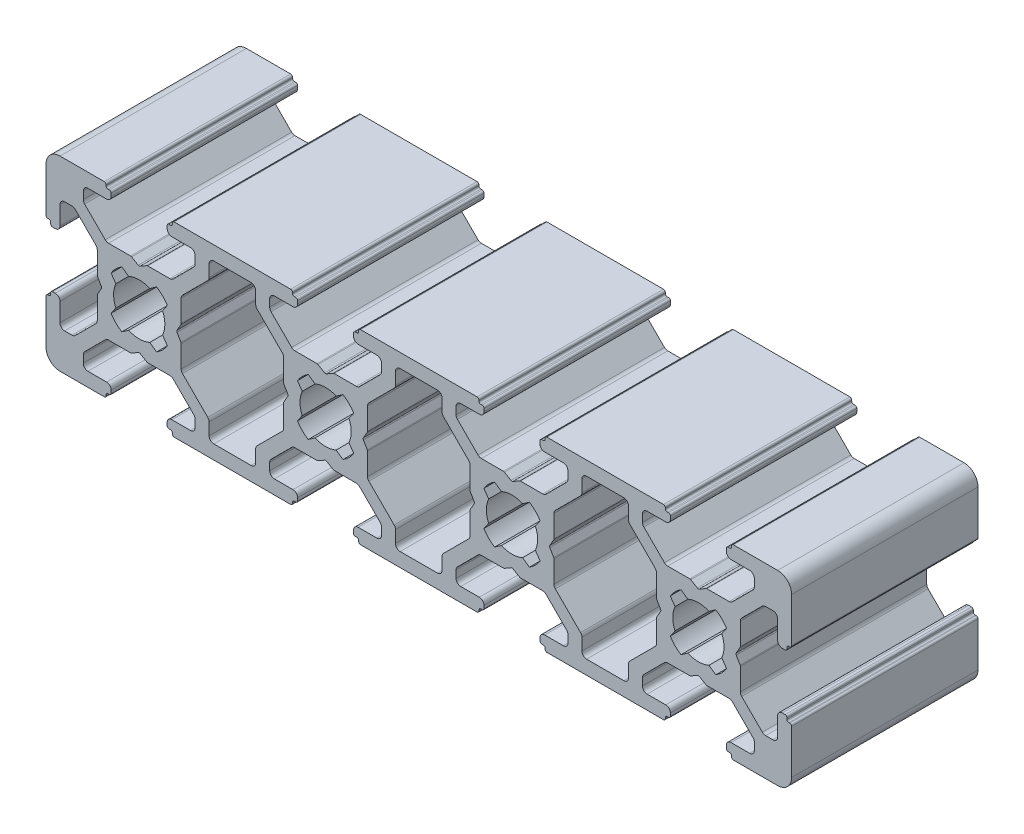
SolidWorks part; units mm, degrees
material "АД31Т ГОСТ 4784-97"
ref_plane "Спереди" through (0, 0, 0) normal (0, 0, 1) x (1, 0, 0)
ref_plane "Сверху" through (0, 0, 0) normal (0, 1, 0) x (1, 0, 0)
ref_plane "Справа" through (0, 0, 0) normal (1, 0, 0) x (0, 0, -1)
sketch "Эскиз1" plane through (0, 0, 0) normal (0, 0, 1) x (1, 0, 0)
  line L0 (3.1454, -5.8536) -> (2.6464, -6.3525)
  line L1 (5.5, 0.9196) -> (5.5, 3.2919)
  line L2 (-13.6454, 4.6464) -> (-15.8536, 6.8546)
  line L3 (-18, 6) -> (-17.2081, 6)
  line L4 (-14.5, 0.9196) -> (-14.5, 3.2919)
  line L5 (-6.3546, -4.6464) -> (-4.1464, -6.8546)
  line L6 (-19.3, 3) -> (-19, 3)
  line L7 (-19.5, 3.35) -> (-19.5, 3.2)
  line L8 (-19.8, 3.55) -> (-19.7, 3.55)
  line L9 (-20, 8.5) -> (-20, 3.75)
  line L10 (-13.0204, 1.8653) -> (-12.5065, 1.1313)
  line L11 (-18.5, 3.5) -> (-18.5, 5.5)
  line L12 (-13.75, 10) -> (-18.5, 10)
  line L13 (-14.6464, 3.6454) -> (-16.8546, 5.8536)
  line L14 (-10.9196, 4.5) -> (-13.2919, 4.5)
  line L15 (-16, 8) -> (-16, 7.2081)
  line L16 (-14.0577, -0.1) -> (-14.4732, -0.8196)
  line L17 (-14.0577, 0.1) -> (-14.4732, 0.8196)
  line L18 (-11.8653, 3.0204) -> (-11.1313, 2.5065)
  line L19 (6.25, 10) -> (-6.25, 10)
  line L20 (-8.1347, 3.0204) -> (-8.8687, 2.5065)
  line L21 (-5.5, -0.9196) -> (-5.5, -3.2919)
  line L22 (-6.7081, 4.5) -> (-9.0804, 4.5)
  line L23 (-2.5, 8) -> (-2.5, 6.7061)
  line L24 (-3.1454, 5.8536) -> (-2.6464, 6.3525)
  line L25 (-10.1, 4.0577) -> (-10.8196, 4.4732)
  line L26 (-6.9796, 1.8653) -> (-7.4935, 1.1313)
  line L27 (-6.9796, -1.8653) -> (-7.4935, -1.1313)
  line L28 (-8.1347, -3.0204) -> (-8.8687, -2.5065)
  line L29 (-11.8653, -3.0204) -> (-11.1313, -2.5065)
  line L30 (-13.0204, -1.8653) -> (-12.5065, -1.1313)
  line L31 (-9.9, 4.0577) -> (-9.1804, 4.4732)
  line L32 (-13.5, 8.5) -> (-15.5, 8.5)
  line L33 (-13.55, 9.8) -> (-13.55, 9.7)
  line L34 (-13.35, 9.5) -> (-13.2, 9.5)
  line L35 (-13, 9.3) -> (-13, 9)
  line L36 (-10.9196, 4.5) -> (-13.2919, 4.5)
  line L37 (2, 8.5) -> (-2, 8.5)
  line L38 (-7, 9.3) -> (-7, 9)
  line L39 (-5.3536, 3.6454) -> (-3.1454, 5.8536)
  line L40 (-4, 8) -> (-4, 7.2081)
  line L41 (-6.3546, 4.6464) -> (-4.1464, 6.8546)
  line L42 (-6.65, 9.5) -> (-6.8, 9.5)
  line L43 (-6.45, 9.8) -> (-6.45, 9.7)
  line L44 (-6.5, 8.5) -> (-4.5, 8.5)
  line L45 (5.9423, -0.1) -> (5.5268, -0.8196)
  line L46 (-6.3546, -4.6464) -> (-4.1464, -6.8546)
  line L47 (-5.3536, -3.6454) -> (-3.1454, -5.8536)
  line L48 (-6.5, -8.5) -> (-4.5, -8.5)
  line L49 (-6.45, -9.8) -> (-6.45, -9.7)
  line L50 (-6.65, -9.5) -> (-6.8, -9.5)
  line L51 (-4, -8) -> (-4, -7.2081)
  line L52 (-5.3536, -3.6454) -> (-3.1454, -5.8536)
  line L53 (-7, -9.3) -> (-7, -9)
  line L54 (2, -8.5) -> (-2, -8.5)
  line L55 (-10.9196, -4.5) -> (-13.2919, -4.5)
  line L56 (-13, -9.3) -> (-13, -9)
  line L57 (-13.35, -9.5) -> (-13.2, -9.5)
  line L58 (-13.55, -9.8) -> (-13.55, -9.7)
  line L59 (-13.5, -8.5) -> (-15.5, -8.5)
  line L60 (-9.9, -4.0577) -> (-9.1804, -4.4732)
  line L61 (-13.0204, 1.8653) -> (-12.5065, 1.1313)
  line L62 (-11.8653, 3.0204) -> (-11.1313, 2.5065)
  line L63 (-8.1347, 3.0204) -> (-8.8687, 2.5065)
  line L64 (-6.9796, 1.8653) -> (-7.4935, 1.1313)
  line L65 (-6.9796, -1.8653) -> (-7.4935, -1.1313)
  line L66 (-10.1, -4.0577) -> (-10.8196, -4.4732)
  line L67 (-2.5, -8) -> (-2.5, -6.7061)
  line L68 (-6.7081, -4.5) -> (-9.0804, -4.5)
  line L69 (-5.9423, 0.1) -> (-5.5268, 0.8196)
  line L70 (-8.1347, -3.0204) -> (-8.8687, -2.5065)
  line L71 (-11.8653, -3.0204) -> (-11.1313, -2.5065)
  line L72 (-14.0577, -0.1) -> (-14.4732, -0.8196)
  line L73 (-14.0577, 0.1) -> (-14.4732, 0.8196)
  line L74 (-16, -8) -> (-16, -7.2081)
  line L75 (-10.9196, -4.5) -> (-13.2919, -4.5)
  line L76 (-14.6464, -3.6454) -> (-16.8546, -5.8536)
  line L77 (-13.75, -10) -> (-18.5, -10)
  line L78 (-18.5, -3.5) -> (-18.5, -5.5)
  line L79 (-13.0204, -1.8653) -> (-12.5065, -1.1313)
  line L80 (-20, -8.5) -> (-20, -3.75)
  line L81 (-19.8, -3.55) -> (-19.7, -3.55)
  line L82 (-19.5, -3.35) -> (-19.5, -3.2)
  line L83 (-19.3, -3) -> (-19, -3)
  line L84 (-14.5, -0.9196) -> (-14.5, -3.2919)
  line L85 (-18, -6) -> (-17.2081, -6)
  line L86 (-13.6454, -4.6464) -> (-15.8536, -6.8546)
  line L87 (6.25, -10) -> (-6.25, -10)
  line L88 (-5.3536, -3.6454) -> (-3.1454, -5.8536)
  line L89 (-5.9423, -0.1) -> (-5.5268, -0.8196)
  line L90 (-5.9423, 0.1) -> (-5.5268, 0.8196)
  line L91 (-5.9423, -0.1) -> (-5.5268, -0.8196)
  line L92 (-5.5, 0.9196) -> (-5.5, 3.2919)
  line L93 (-3.1454, -5.8536) -> (-2.6464, -6.3525)
  line L94 (5.9423, 0.1) -> (5.5268, 0.8196)
  line L95 (5.9423, -0.1) -> (5.5268, -0.8196)
  line L96 (5.3536, -3.6454) -> (3.1454, -5.8536)
  line L97 (13.6454, -4.6464) -> (15.8536, -6.8546)
  line L99 (14.5, -0.9196) -> (14.5, -3.2919)
  line L100 (13.75, 10) -> (26.25, 10)
  line L101 (13.75, -10) -> (26.25, -10)
  line L102 (13.6454, -4.6464) -> (15.8536, -6.8546)
  line L103 (14.5, -0.9196) -> (14.5, -3.2919)
  line L104 (13.0204, -1.8653) -> (12.5065, -1.1313)
  line L105 (17.5, 8) -> (17.5, 6.7061)
  line L106 (16.8546, 5.8536) -> (17.3536, 6.3525)
  line L107 (14.6464, -3.6454) -> (16.8546, -5.8536)
  line L108 (10.9196, -4.5) -> (13.2919, -4.5)
  line L109 (13.0204, 1.8653) -> (12.5065, 1.1313)
  line L110 (14.0577, 0.1) -> (14.4732, 0.8196)
  line L111 (14.0577, -0.1) -> (14.4732, -0.8196)
  line L112 (11.8653, -3.0204) -> (11.1313, -2.5065)
  line L113 (8.1347, -3.0204) -> (8.8687, -2.5065)
  line L114 (5.9423, 0.1) -> (5.5268, 0.8196)
  line L115 (6.7081, -4.5) -> (9.0804, -4.5)
  line L116 (2.5, -8) -> (2.5, -6.7061)
  line L117 (10.1, -4.0577) -> (10.8196, -4.4732)
  line L118 (6.9796, -1.8653) -> (7.4935, -1.1313)
  line L119 (6.9796, 1.8653) -> (7.4935, 1.1313)
  line L120 (8.1347, 3.0204) -> (8.8687, 2.5065)
  line L121 (11.8653, 3.0204) -> (11.1313, 2.5065)
  line L122 (13.0204, 1.8653) -> (12.5065, 1.1313)
  line L123 (9.9, -4.0577) -> (9.1804, -4.4732)
  line L124 (13.0204, -1.8653) -> (12.5065, -1.1313)
  line L125 (13, 9.3) -> (13, 9)
  line L126 (14.6464, 3.6454) -> (16.8546, 5.8536)
  line L127 (16, 8) -> (16, 7.2081)
  line L128 (10.9196, -4.5) -> (13.2919, -4.5)
  line L129 (7, -9.3) -> (7, -9)
  line L130 (5.3536, -3.6454) -> (3.1454, -5.8536)
  line L131 (4, -8) -> (4, -7.2081)
  line L132 (6.65, -9.5) -> (6.8, -9.5)
  line L133 (6.45, -9.8) -> (6.45, -9.7)
  line L134 (6.5, -8.5) -> (4.5, -8.5)
  line L135 (5.3536, -3.6454) -> (3.1454, -5.8536)
  line L136 (6.3546, -4.6464) -> (4.1464, -6.8546)
  line L137 (6.5, 8.5) -> (4.5, 8.5)
  line L138 (6.45, 9.8) -> (6.45, 9.7)
  line L139 (6.65, 9.5) -> (6.8, 9.5)
  line L140 (6.3546, 4.6464) -> (4.1464, 6.8546)
  line L141 (4, 8) -> (4, 7.2081)
  line L142 (5.3536, 3.6454) -> (3.1454, 5.8536)
  line L143 (7, 9.3) -> (7, 9)
  line L144 (10.9196, 4.5) -> (13.2919, 4.5)
  line L145 (13.6454, 4.6464) -> (15.8536, 6.8546)
  line L146 (13.35, 9.5) -> (13.2, 9.5)
  line L147 (13.55, 9.8) -> (13.55, 9.7)
  line L148 (13.5, 8.5) -> (15.5, 8.5)
  line L149 (9.9, 4.0577) -> (9.1804, 4.4732)
  line L150 (13.0204, -1.8653) -> (12.5065, -1.1313)
  line L151 (11.8653, -3.0204) -> (11.1313, -2.5065)
  line L152 (8.1347, -3.0204) -> (8.8687, -2.5065)
  line L153 (6.9796, -1.8653) -> (7.4935, -1.1313)
  line L154 (6.9796, 1.8653) -> (7.4935, 1.1313)
  line L155 (10.1, 4.0577) -> (10.8196, 4.4732)
  line L156 (3.1454, 5.8536) -> (2.6464, 6.3525)
  line L157 (2.5, 8) -> (2.5, 6.7061)
  line L158 (6.7081, 4.5) -> (9.0804, 4.5)
  line L159 (5.5, -0.9196) -> (5.5, -3.2919)
  line L160 (8.1347, 3.0204) -> (8.8687, 2.5065)
  line L161 (11.8653, 3.0204) -> (11.1313, 2.5065)
  line L162 (14.0577, 0.1) -> (14.4732, 0.8196)
  line L163 (14.0577, -0.1) -> (14.4732, -0.8196)
  line L164 (13.6454, -4.6464) -> (15.8536, -6.8546)
  line L165 (10.9196, 4.5) -> (13.2919, 4.5)
  line L166 (14.6464, 3.6454) -> (16.8546, 5.8536)
  line L167 (14.6464, -3.6454) -> (16.8546, -5.8536)
  line L168 (13.5, -8.5) -> (15.5, -8.5)
  line L169 (13.0204, 1.8653) -> (12.5065, 1.1313)
  line L170 (13.55, -9.8) -> (13.55, -9.7)
  line L171 (13.35, -9.5) -> (13.2, -9.5)
  line L172 (16, -8) -> (16, -7.2081)
  line L173 (14.6464, -3.6454) -> (16.8546, -5.8536)
  line L174 (6.3546, -4.6464) -> (4.1464, -6.8546)
  line L175 (14.5, 0.9196) -> (14.5, 3.2919)
  line L176 (13, -9.3) -> (13, -9)
  line L177 (13.6454, 4.6464) -> (15.8536, 6.8546)
  line L178 (13.0204, 1.8653) -> (12.5065, 1.1313)
  line L179 (13.0204, -1.8653) -> (12.5065, -1.1313)
  line L180 (17.5, -8) -> (17.5, -6.7061)
  line L181 (14.0577, 0.1) -> (14.4732, 0.8196)
  line L182 (14.6464, -3.6454) -> (16.8546, -5.8536)
  line L183 (14.0577, -0.1) -> (14.4732, -0.8196)
  line L184 (14.0577, 0.1) -> (14.4732, 0.8196)
  line L185 (18, -8.5) -> (22, -8.5)
  line L186 (14.0577, -0.1) -> (14.4732, -0.8196)
  line L187 (18, 8.5) -> (22, 8.5)
  line L188 (14.5, 0.9196) -> (14.5, 3.2919)
  line L189 (16.8546, -5.8536) -> (17.3536, -6.3525)
  line L190 (23.1454, -5.8536) -> (22.6464, -6.3525)
  line L191 (25.5, 0.9196) -> (25.5, 3.2919)
  line L192 (25.9423, -0.1) -> (25.5268, -0.8196)
  line L193 (25.9423, 0.1) -> (25.5268, 0.8196)
  line L194 (25.9423, -0.1) -> (25.5268, -0.8196)
  line L195 (25.3536, -3.6454) -> (23.1454, -5.8536)
  line L196 (25.9423, 0.1) -> (25.5268, 0.8196)
  line L197 (22.5, -8) -> (22.5, -6.7061)
  line L198 (26.9796, -1.8653) -> (27.4935, -1.1313)
  line L199 (26.9796, 1.8653) -> (27.4935, 1.1313)
  line L200 (26.3546, 4.6464) -> (24.1464, 6.8546)
  line L201 (27, -9.3) -> (27, -9)
  line L202 (25.5, 0.9196) -> (25.5, 3.2919)
  line L203 (33.6454, -4.6464) -> (35.8536, -6.8546)
  line L204 (25.3536, -3.6454) -> (23.1454, -5.8536)
  line L205 (24, -8) -> (24, -7.2081)
  line L206 (26.65, -9.5) -> (26.8, -9.5)
  line L207 (26.45, -9.8) -> (26.45, -9.7)
  line L208 (26.9796, 1.8653) -> (27.4935, 1.1313)
  line L209 (26.5, -8.5) -> (24.5, -8.5)
  line L210 (25.3536, -3.6454) -> (23.1454, -5.8536)
  line L211 (25.3536, 3.6454) -> (23.1454, 5.8536)
  line L212 (29.0804, 4.5) -> (26.7081, 4.5)
  line L213 (26.3546, -4.6464) -> (24.1464, -6.8546)
  line L214 (25.9423, -0.1) -> (25.5268, -0.8196)
  line L215 (25.9423, 0.1) -> (25.5268, 0.8196)
  line L216 (28.1347, 3.0204) -> (28.8687, 2.5065)
  line L217 (31.8653, 3.0204) -> (31.1313, 2.5065)
  line L218 (34.5, -0.9196) -> (34.5, -3.2919)
  line L219 (33.2919, 4.5) -> (30.9196, 4.5)
  line L220 (37.5, 8) -> (37.5, 6.7061)
  line L221 (36.8546, 5.8536) -> (37.3536, 6.3525)
  line L222 (29.9, 4.0577) -> (29.1804, 4.4732)
  line L223 (33.0204, 1.8653) -> (32.5065, 1.1313)
  line L224 (33.0204, -1.8653) -> (32.5065, -1.1313)
  line L225 (31.8653, -3.0204) -> (31.1313, -2.5065)
  line L226 (28.1347, -3.0204) -> (28.8687, -2.5065)
  line L227 (26.9796, -1.8653) -> (27.4935, -1.1313)
  line L228 (30.1, 4.0577) -> (30.8196, 4.4732)
  line L229 (26.5, 8.5) -> (24.5, 8.5)
  line L230 (26.45, 9.8) -> (26.45, 9.7)
  line L231 (26.65, 9.5) -> (26.8, 9.5)
  line L232 (26.3546, 4.6464) -> (24.1464, 6.8546)
  line L233 (29.0804, 4.5) -> (26.7081, 4.5)
  line L234 (33, 9.3) -> (33, 9)
  line L235 (34.6464, 3.6454) -> (36.8546, 5.8536)
  line L236 (36, 8) -> (36, 7.2081)
  line L237 (33.6454, 4.6464) -> (35.8536, 6.8546)
  line L238 (33.35, 9.5) -> (33.2, 9.5)
  line L239 (33.55, 9.8) -> (33.55, 9.7)
  line L240 (33.5, 8.5) -> (35.5, 8.5)
  line L241 (33.6454, -4.6464) -> (35.8536, -6.8546)
  line L242 (34.6464, -3.6454) -> (36.8546, -5.8536)
  line L243 (33.5, -8.5) -> (35.5, -8.5)
  line L244 (33.55, -9.8) -> (33.55, -9.7)
  line L245 (33.35, -9.5) -> (33.2, -9.5)
  line L246 (36, -8) -> (36, -7.2081)
  line L247 (34.6464, -3.6454) -> (36.8546, -5.8536)
  line L248 (33, -9.3) -> (33, -9)
  line L249 (29.0804, -4.5) -> (26.7081, -4.5)
  line L250 (24, 8) -> (24, 7.2081)
  line L251 (25.3536, 3.6454) -> (23.1454, 5.8536)
  line L252 (27, 9.3) -> (27, 9)
  line L253 (26.9796, -1.8653) -> (27.4935, -1.1313)
  line L254 (30.1, -4.0577) -> (30.8196, -4.4732)
  line L255 (26.9796, 1.8653) -> (27.4935, 1.1313)
  line L256 (28.1347, 3.0204) -> (28.8687, 2.5065)
  line L257 (31.8653, 3.0204) -> (31.1313, 2.5065)
  line L258 (33.0204, 1.8653) -> (32.5065, 1.1313)
  line L259 (33.0204, -1.8653) -> (32.5065, -1.1313)
  line L260 (29.9, -4.0577) -> (29.1804, -4.4732)
  line L261 (37.5, -8) -> (37.5, -6.7061)
  line L262 (33.2919, -4.5) -> (30.9196, -4.5)
  line L263 (34.0577, 0.1) -> (34.4732, 0.8196)
  line L264 (31.8653, -3.0204) -> (31.1313, -2.5065)
  line L265 (28.1347, -3.0204) -> (28.8687, -2.5065)
  line L266 (25.9423, -0.1) -> (25.5268, -0.8196)
  line L267 (25.9423, 0.1) -> (25.5268, 0.8196)
  line L268 (26.9796, 1.8653) -> (27.4935, 1.1313)
  line L269 (29.0804, -4.5) -> (26.7081, -4.5)
  line L270 (25.3536, -3.6454) -> (23.1454, -5.8536)
  line L271 (23.1454, 5.8536) -> (22.6464, 6.3525)
  line L272 (22.5, 8) -> (22.5, 6.7061)
  line L273 (26.9796, -1.8653) -> (27.4935, -1.1313)
  line L274 (25.5, -0.9196) -> (25.5, -3.2919)
  line L275 (26.3546, -4.6464) -> (24.1464, -6.8546)
  line L276 (25.5, -0.9196) -> (25.5, -3.2919)
  line L277 (26.3546, -4.6464) -> (24.1464, -6.8546)
  line L278 (34.6464, -3.6454) -> (36.8546, -5.8536)
  line L279 (34.0577, -0.1) -> (34.4732, -0.8196)
  line L280 (34.0577, 0.1) -> (34.4732, 0.8196)
  line L281 (43.1454, -5.8536) -> (42.6464, -6.3525)
  line L282 (45.5, 0.9196) -> (45.5, 3.2919)
  line L283 (45.9423, -0.1) -> (45.5268, -0.8196)
  line L284 (45.9423, 0.1) -> (45.5268, 0.8196)
  line L285 (45.9423, -0.1) -> (45.5268, -0.8196)
  line L286 (45.3536, -3.6454) -> (43.1454, -5.8536)
  line L287 (33.75, -10) -> (46.25, -10)
  line L288 (53.6454, -4.6464) -> (55.8536, -6.8546)
  line L289 (58, -6) -> (57.2081, -6)
  line L290 (54.5, -0.9196) -> (54.5, -3.2919)
  line L291 (59.3, -3) -> (59, -3)
  line L292 (59.5, -3.35) -> (59.5, -3.2)
  line L293 (59.8, -3.55) -> (59.7, -3.55)
  line L294 (60, -8.5) -> (60, -3.75)
  line L295 (53.0204, -1.8653) -> (52.5065, -1.1313)
  line L296 (58.5, -3.5) -> (58.5, -5.5)
  line L297 (53.75, -10) -> (58.5, -10)
  line L298 (54.6464, -3.6454) -> (56.8546, -5.8536)
  line L299 (50.9196, -4.5) -> (53.2919, -4.5)
  line L300 (56, -8) -> (56, -7.2081)
  line L301 (54.0577, 0.1) -> (54.4732, 0.8196)
  line L302 (54.0577, -0.1) -> (54.4732, -0.8196)
  line L303 (51.8653, -3.0204) -> (51.1313, -2.5065)
  line L304 (48.1347, -3.0204) -> (48.8687, -2.5065)
  line L305 (45.9423, 0.1) -> (45.5268, 0.8196)
  line L306 (46.7081, -4.5) -> (49.0804, -4.5)
  line L307 (42.5, -8) -> (42.5, -6.7061)
  line L308 (50.1, -4.0577) -> (50.8196, -4.4732)
  line L309 (46.9796, -1.8653) -> (47.4935, -1.1313)
  line L310 (46.9796, 1.8653) -> (47.4935, 1.1313)
  line L311 (48.1347, 3.0204) -> (48.8687, 2.5065)
  line L312 (51.8653, 3.0204) -> (51.1313, 2.5065)
  line L313 (53.0204, 1.8653) -> (52.5065, 1.1313)
  line L314 (49.9, -4.0577) -> (49.1804, -4.4732)
  line L315 (53.5, -8.5) -> (55.5, -8.5)
  line L316 (53.55, -9.8) -> (53.55, -9.7)
  line L317 (53.35, -9.5) -> (53.2, -9.5)
  line L318 (53, -9.3) -> (53, -9)
  line L319 (50.9196, -4.5) -> (53.2919, -4.5)
  line L320 (38, -8.5) -> (42, -8.5)
  line L321 (47, -9.3) -> (47, -9)
  line L322 (45.3536, -3.6454) -> (43.1454, -5.8536)
  line L323 (44, -8) -> (44, -7.2081)
  line L324 (46.65, -9.5) -> (46.8, -9.5)
  line L325 (46.45, -9.8) -> (46.45, -9.7)
  line L326 (46.5, -8.5) -> (44.5, -8.5)
  line L327 (45.3536, -3.6454) -> (43.1454, -5.8536)
  line L328 (46.3546, -4.6464) -> (44.1464, -6.8546)
  line L329 (34.0577, -0.1) -> (34.4732, -0.8196)
  line L330 (46.5, 8.5) -> (44.5, 8.5)
  line L331 (46.45, 9.8) -> (46.45, 9.7)
  line L332 (46.65, 9.5) -> (46.8, 9.5)
  line L333 (46.3546, 4.6464) -> (44.1464, 6.8546)
  line L334 (44, 8) -> (44, 7.2081)
  line L335 (45.3536, 3.6454) -> (43.1454, 5.8536)
  line L336 (47, 9.3) -> (47, 9)
  line L337 (38, 8.5) -> (42, 8.5)
  line L338 (50.9196, 4.5) -> (53.2919, 4.5)
  line L339 (53, 9.3) -> (53, 9)
  line L340 (53.35, 9.5) -> (53.2, 9.5)
  line L341 (53.55, 9.8) -> (53.55, 9.7)
  line L342 (53.5, 8.5) -> (55.5, 8.5)
  line L343 (49.9, 4.0577) -> (49.1804, 4.4732)
  line L344 (53.0204, -1.8653) -> (52.5065, -1.1313)
  line L345 (51.8653, -3.0204) -> (51.1313, -2.5065)
  line L346 (48.1347, -3.0204) -> (48.8687, -2.5065)
  line L347 (46.9796, -1.8653) -> (47.4935, -1.1313)
  line L348 (46.9796, 1.8653) -> (47.4935, 1.1313)
  line L349 (50.1, 4.0577) -> (50.8196, 4.4732)
  line L350 (43.1454, 5.8536) -> (42.6464, 6.3525)
  line L351 (42.5, 8) -> (42.5, 6.7061)
  line L352 (46.7081, 4.5) -> (49.0804, 4.5)
  line L353 (45.5, -0.9196) -> (45.5, -3.2919)
  line L354 (48.1347, 3.0204) -> (48.8687, 2.5065)
  line L355 (33.75, 10) -> (46.25, 10)
  line L356 (51.8653, 3.0204) -> (51.1313, 2.5065)
  line L357 (54.0577, 0.1) -> (54.4732, 0.8196)
  line L358 (54.0577, -0.1) -> (54.4732, -0.8196)
  line L359 (56, 8) -> (56, 7.2081)
  line L360 (50.9196, 4.5) -> (53.2919, 4.5)
  line L361 (54.6464, 3.6454) -> (56.8546, 5.8536)
  line L362 (53.75, 10) -> (58.5, 10)
  line L363 (58.5, 3.5) -> (58.5, 5.5)
  line L364 (53.0204, 1.8653) -> (52.5065, 1.1313)
  line L365 (60, 8.5) -> (60, 3.75)
  line L366 (59.8, 3.55) -> (59.7, 3.55)
  line L367 (59.5, 3.35) -> (59.5, 3.2)
  line L368 (59.3, 3) -> (59, 3)
  line L369 (46.3546, -4.6464) -> (44.1464, -6.8546)
  line L370 (54.5, 0.9196) -> (54.5, 3.2919)
  line L371 (58, 6) -> (57.2081, 6)
  line L372 (53.6454, 4.6464) -> (55.8536, 6.8546)
  line L373 (34.5, 0.9196) -> (34.5, 3.2919)
  line L374 (36.8546, -5.8536) -> (37.3536, -6.3525)
  arc A0 (-17.2081, 6) -> (-16.8546, 5.8536) centre (-17.2081, 5.5) cw
  arc A1 (-14.5, 3.2919) -> (-14.6464, 3.6454) centre (-15, 3.2919) ccw
  arc A2 (-16, 7.2081) -> (-15.8536, 6.8546) centre (-15.5, 7.2081) ccw
  arc A3 (-18.5, 10) -> (-20, 8.5) centre (-18.5, 8.5) ccw
  arc A4 (-19.7, 3.55) -> (-19.5, 3.35) centre (-19.7, 3.35) cw
  arc A5 (-20, 3.75) -> (-19.8, 3.55) centre (-19.8, 3.75) ccw
  arc A6 (-19.5, 3.2) -> (-19.3, 3) centre (-19.3, 3.2) ccw
  arc A7 (-19, 3) -> (-18.5, 3.5) centre (-19, 3.5) ccw
  arc A8 (-18, 6) -> (-18.5, 5.5) centre (-18, 5.5) ccw
  arc A9 (-13.2919, 4.5) -> (-13.6454, 4.6464) centre (-13.2919, 5) cw
  arc A10 (-14.4732, -0.8196) -> (-14.5, -0.9196) centre (-14.3, -0.9196) ccw
  arc A11 (-14.4732, 0.8196) -> (-14.5, 0.9196) centre (-14.3, 0.9196) cw
  arc A12 (-14.0577, 0.1) -> (-14.0577, -0.1) centre (-14.2309, 0) cw
  arc A13 (-10.1, 4.0577) -> (-9.9, 4.0577) centre (-10, 4.2309) ccw
  arc A14 (-13.0204, -1.8653) -> (-11.8653, -3.0204) centre (-10, 0) ccw
  arc A15 (-12.5065, 1.1313) -> (-12.5065, -1.1313) centre (-10, 0) ccw
  arc A16 (-8.8687, 2.5065) -> (-11.1313, 2.5065) centre (-10, 0) ccw
  arc A17 (-7.4935, -1.1313) -> (-7.4935, 1.1313) centre (-10, 0) ccw
  arc A18 (-11.1313, -2.5065) -> (-8.8687, -2.5065) centre (-10, 0) ccw
  arc A19 (-11.8653, 3.0204) -> (-13.0204, 1.8653) centre (-10, 0) ccw
  arc A20 (-6.9796, 1.8653) -> (-8.1347, 3.0204) centre (-10, 0) ccw
  arc A21 (-8.1347, -3.0204) -> (-6.9796, -1.8653) centre (-10, 0) ccw
  arc A22 (-10.8196, 4.4732) -> (-10.9196, 4.5) centre (-10.9196, 4.3) ccw
  arc A23 (-9.1804, 4.4732) -> (-9.0804, 4.5) centre (-9.0804, 4.3) cw
  arc A24 (-16, 8) -> (-15.5, 8.5) centre (-15.5, 8) cw
  arc A25 (-13, 9) -> (-13.5, 8.5) centre (-13.5, 9) cw
  arc A26 (-13.2, 9.5) -> (-13, 9.3) centre (-13.2, 9.3) cw
  arc A27 (-13.75, 10) -> (-13.55, 9.8) centre (-13.75, 9.8) cw
  arc A28 (-13.55, 9.7) -> (-13.35, 9.5) centre (-13.35, 9.7) ccw
  arc A29 (-6.45, 9.7) -> (-6.65, 9.5) centre (-6.65, 9.7) cw
  arc A30 (-6.25, 10) -> (-6.45, 9.8) centre (-6.25, 9.8) ccw
  arc A31 (-6.8, 9.5) -> (-7, 9.3) centre (-6.8, 9.3) ccw
  arc A32 (-7, 9) -> (-6.5, 8.5) centre (-6.5, 9) ccw
  arc A33 (-2, 8.5) -> (-2.5, 8) centre (-2, 8) ccw
  arc A34 (-6.7081, 4.5) -> (-6.3546, 4.6464) centre (-6.7081, 5) ccw
  arc A35 (-2.6464, 6.3525) -> (-2.5, 6.7061) centre (-3, 6.7061) ccw
  arc A36 (-4.1464, 6.8546) -> (-4, 7.2081) centre (-4.5, 7.2081) ccw
  arc A37 (-4.5, 8.5) -> (-4, 8) centre (-4.5, 8) cw
  arc A38 (-5.5, -3.2919) -> (-5.3536, -3.6454) centre (-5, -3.2919) ccw
  arc A39 (-4.5, -8.5) -> (-4, -8) centre (-4.5, -8) ccw
  arc A40 (-4.1464, -6.8546) -> (-4, -7.2081) centre (-4.5, -7.2081) cw
  arc A41 (-2, -8.5) -> (-2.5, -8) centre (-2, -8) cw
  arc A42 (-5.5, 3.2919) -> (-5.3536, 3.6454) centre (-5, 3.2919) cw
  arc A43 (-7, -9) -> (-6.5, -8.5) centre (-6.5, -9) cw
  arc A44 (-6.8, -9.5) -> (-7, -9.3) centre (-6.8, -9.3) cw
  arc A45 (-5.5, -3.2919) -> (-5.3536, -3.6454) centre (-5, -3.2919) ccw
  arc A46 (-6.25, -10) -> (-6.45, -9.8) centre (-6.25, -9.8) cw
  arc A47 (-6.45, -9.7) -> (-6.65, -9.5) centre (-6.65, -9.7) ccw
  arc A48 (-2.6464, -6.3525) -> (-2.5, -6.7061) centre (-3, -6.7061) cw
  arc A49 (5.5268, -0.8196) -> (5.5, -0.9196) centre (5.7, -0.9196) ccw
  arc A50 (5.5268, 0.8196) -> (5.5, 0.9196) centre (5.7, 0.9196) cw
  arc A51 (5.9423, 0.1) -> (5.9423, -0.1) centre (5.7691, 0) cw
  arc A52 (5.5268, -0.8196) -> (5.5, -0.9196) centre (5.7, -0.9196) ccw
  arc A53 (-6.7081, -4.5) -> (-6.3546, -4.6464) centre (-6.7081, -5) cw
  arc A54 (5.5268, 0.8196) -> (5.5, 0.9196) centre (5.7, 0.9196) cw
  arc A55 (12.5065, -1.1313) -> (12.5065, 1.1313) centre (10, 0) ccw
  arc A56 (14.5, -3.2919) -> (14.6464, -3.6454) centre (15, -3.2919) ccw
  arc A57 (13.0204, 1.8653) -> (11.8653, 3.0204) centre (10, 0) ccw
  arc A58 (11.8653, -3.0204) -> (13.0204, -1.8653) centre (10, 0) ccw
  arc A59 (-13.55, -9.7) -> (-13.35, -9.5) centre (-13.35, -9.7) cw
  arc A60 (-13.75, -10) -> (-13.55, -9.8) centre (-13.75, -9.8) ccw
  arc A61 (-13.2, -9.5) -> (-13, -9.3) centre (-13.2, -9.3) ccw
  arc A62 (-13, -9) -> (-13.5, -8.5) centre (-13.5, -9) ccw
  arc A63 (-16, -8) -> (-15.5, -8.5) centre (-15.5, -8) ccw
  arc A64 (-9.1804, -4.4732) -> (-9.0804, -4.5) centre (-9.0804, -4.3) ccw
  arc A65 (-10.8196, -4.4732) -> (-10.9196, -4.5) centre (-10.9196, -4.3) cw
  arc A66 (-8.1347, 3.0204) -> (-6.9796, 1.8653) centre (-10, 0) cw
  arc A67 (-6.9796, -1.8653) -> (-8.1347, -3.0204) centre (-10, 0) cw
  arc A68 (-11.8653, -3.0204) -> (-13.0204, -1.8653) centre (-10, 0) cw
  arc A69 (-11.1313, 2.5065) -> (-8.8687, 2.5065) centre (-10, 0) cw
  arc A70 (-8.8687, -2.5065) -> (-11.1313, -2.5065) centre (-10, 0) cw
  arc A71 (-13.0204, 1.8653) -> (-11.8653, 3.0204) centre (-10, 0) cw
  arc A72 (-10.1, -4.0577) -> (-9.9, -4.0577) centre (-10, -4.2309) cw
  arc A73 (-14.4732, -0.8196) -> (-14.5, -0.9196) centre (-14.3, -0.9196) ccw
  arc A74 (-14.4732, 0.8196) -> (-14.5, 0.9196) centre (-14.3, 0.9196) cw
  arc A75 (-13.2919, -4.5) -> (-13.6454, -4.6464) centre (-13.2919, -5) ccw
  arc A76 (-18, -6) -> (-18.5, -5.5) centre (-18, -5.5) cw
  arc A77 (-19, -3) -> (-18.5, -3.5) centre (-19, -3.5) cw
  arc A78 (-19.5, -3.2) -> (-19.3, -3) centre (-19.3, -3.2) cw
  arc A79 (-20, -3.75) -> (-19.8, -3.55) centre (-19.8, -3.75) cw
  arc A80 (-19.7, -3.55) -> (-19.5, -3.35) centre (-19.7, -3.35) ccw
  arc A81 (-18.5, -10) -> (-20, -8.5) centre (-18.5, -8.5) cw
  arc A82 (-16, -7.2081) -> (-15.8536, -6.8546) centre (-15.5, -7.2081) cw
  arc A83 (-14.5, -3.2919) -> (-14.6464, -3.6454) centre (-15, -3.2919) cw
  arc A84 (-17.2081, -6) -> (-16.8546, -5.8536) centre (-17.2081, -5.5) ccw
  arc A85 (-5.5268, 0.8196) -> (-5.5, 0.9196) centre (-5.7, 0.9196) ccw
  arc A86 (-5.5268, -0.8196) -> (-5.5, -0.9196) centre (-5.7, -0.9196) cw
  arc A87 (-5.9423, 0.1) -> (-5.9423, -0.1) centre (-5.7691, 0) ccw
  arc A88 (-5.5268, 0.8196) -> (-5.5, 0.9196) centre (-5.7, 0.9196) ccw
  arc A89 (-5.5268, -0.8196) -> (-5.5, -0.9196) centre (-5.7, -0.9196) cw
  arc A90 (13.55, 9.7) -> (13.35, 9.5) centre (13.35, 9.7) cw
  arc A91 (13.75, 10) -> (13.55, 9.8) centre (13.75, 9.8) ccw
  arc A92 (13.2, 9.5) -> (13, 9.3) centre (13.2, 9.3) ccw
  arc A93 (13, 9) -> (13.5, 8.5) centre (13.5, 9) ccw
  arc A94 (18, 8.5) -> (17.5, 8) centre (18, 8) ccw
  arc A95 (13.2919, -4.5) -> (13.6454, -4.6464) centre (13.2919, -5) cw
  arc A96 (14.4732, 0.8196) -> (14.5, 0.9196) centre (14.3, 0.9196) ccw
  arc A97 (14.4732, -0.8196) -> (14.5, -0.9196) centre (14.3, -0.9196) cw
  arc A98 (10.1, -4.0577) -> (9.9, -4.0577) centre (10, -4.2309) ccw
  arc A99 (13.0204, 1.8653) -> (11.8653, 3.0204) centre (10, 0) ccw
  arc A100 (8.8687, -2.5065) -> (11.1313, -2.5065) centre (10, 0) ccw
  arc A101 (11.1313, 2.5065) -> (8.8687, 2.5065) centre (10, 0) ccw
  arc A102 (11.8653, -3.0204) -> (13.0204, -1.8653) centre (10, 0) ccw
  arc A103 (6.9796, -1.8653) -> (8.1347, -3.0204) centre (10, 0) ccw
  arc A104 (8.1347, 3.0204) -> (6.9796, 1.8653) centre (10, 0) ccw
  arc A105 (10.8196, -4.4732) -> (10.9196, -4.5) centre (10.9196, -4.3) ccw
  arc A106 (9.1804, -4.4732) -> (9.0804, -4.5) centre (9.0804, -4.3) cw
  arc A107 (13.2919, 4.5) -> (13.6454, 4.6464) centre (13.2919, 5) ccw
  arc A108 (17.3536, 6.3525) -> (17.5, 6.7061) centre (17, 6.7061) ccw
  arc A109 (15.8536, 6.8546) -> (16, 7.2081) centre (15.5, 7.2081) ccw
  arc A110 (15.5, 8.5) -> (16, 8) centre (15.5, 8) cw
  arc A111 (14.5, -3.2919) -> (14.6464, -3.6454) centre (15, -3.2919) ccw
  arc A112 (6.7081, -4.5) -> (6.3546, -4.6464) centre (6.7081, -5) ccw
  arc A113 (2.6464, -6.3525) -> (2.5, -6.7061) centre (3, -6.7061) ccw
  arc A114 (6.45, -9.7) -> (6.65, -9.5) centre (6.65, -9.7) cw
  arc A115 (6.25, -10) -> (6.45, -9.8) centre (6.25, -9.8) ccw
  arc A116 (5.5, -3.2919) -> (5.3536, -3.6454) centre (5, -3.2919) cw
  arc A117 (6.8, -9.5) -> (7, -9.3) centre (6.8, -9.3) ccw
  arc A118 (7, -9) -> (6.5, -8.5) centre (6.5, -9) ccw
  arc A119 (5.5, 3.2919) -> (5.3536, 3.6454) centre (5, 3.2919) ccw
  arc A120 (2, -8.5) -> (2.5, -8) centre (2, -8) ccw
  arc A121 (4.1464, -6.8546) -> (4, -7.2081) centre (4.5, -7.2081) ccw
  arc A122 (4.5, -8.5) -> (4, -8) centre (4.5, -8) cw
  arc A123 (5.5, -3.2919) -> (5.3536, -3.6454) centre (5, -3.2919) cw
  arc A124 (4.5, 8.5) -> (4, 8) centre (4.5, 8) ccw
  arc A125 (4.1464, 6.8546) -> (4, 7.2081) centre (4.5, 7.2081) cw
  arc A126 (2.6464, 6.3525) -> (2.5, 6.7061) centre (3, 6.7061) cw
  arc A127 (6.7081, 4.5) -> (6.3546, 4.6464) centre (6.7081, 5) cw
  arc A128 (2, 8.5) -> (2.5, 8) centre (2, 8) cw
  arc A129 (7, 9) -> (6.5, 8.5) centre (6.5, 9) cw
  arc A130 (6.8, 9.5) -> (7, 9.3) centre (6.8, 9.3) cw
  arc A131 (6.25, 10) -> (6.45, 9.8) centre (6.25, 9.8) cw
  arc A132 (6.45, 9.7) -> (6.65, 9.5) centre (6.65, 9.7) ccw
  arc A133 (15.5, -8.5) -> (16, -8) centre (15.5, -8) ccw
  arc A134 (15.8536, -6.8546) -> (16, -7.2081) centre (15.5, -7.2081) cw
  arc A135 (18, -8.5) -> (17.5, -8) centre (18, -8) cw
  arc A136 (14.5, 3.2919) -> (14.6464, 3.6454) centre (15, 3.2919) cw
  arc A137 (13, -9) -> (13.5, -8.5) centre (13.5, -9) cw
  arc A138 (9.1804, 4.4732) -> (9.0804, 4.5) centre (9.0804, 4.3) ccw
  arc A139 (10.8196, 4.4732) -> (10.9196, 4.5) centre (10.9196, 4.3) cw
  arc A140 (8.1347, -3.0204) -> (6.9796, -1.8653) centre (10, 0) cw
  arc A141 (6.9796, 1.8653) -> (8.1347, 3.0204) centre (10, 0) cw
  arc A142 (11.8653, 3.0204) -> (13.0204, 1.8653) centre (10, 0) cw
  arc A143 (11.1313, -2.5065) -> (8.8687, -2.5065) centre (10, 0) cw
  arc A144 (7.4935, -1.1313) -> (7.4935, 1.1313) centre (10, 0) cw
  arc A145 (8.8687, 2.5065) -> (11.1313, 2.5065) centre (10, 0) cw
  arc A146 (12.5065, 1.1313) -> (12.5065, -1.1313) centre (10, 0) cw
  arc A147 (13.0204, -1.8653) -> (11.8653, -3.0204) centre (10, 0) cw
  arc A148 (10.1, 4.0577) -> (9.9, 4.0577) centre (10, 4.2309) cw
  arc A149 (14.0577, 0.1) -> (14.0577, -0.1) centre (14.2309, 0) ccw
  arc A150 (14.4732, 0.8196) -> (14.5, 0.9196) centre (14.3, 0.9196) ccw
  arc A151 (14.4732, -0.8196) -> (14.5, -0.9196) centre (14.3, -0.9196) cw
  arc A152 (13.2919, 4.5) -> (13.6454, 4.6464) centre (13.2919, 5) ccw
  arc A153 (13.2, -9.5) -> (13, -9.3) centre (13.2, -9.3) cw
  arc A154 (14.5, -3.2919) -> (14.6464, -3.6454) centre (15, -3.2919) ccw
  arc A155 (13.75, -10) -> (13.55, -9.8) centre (13.75, -9.8) cw
  arc A156 (13.55, -9.7) -> (13.35, -9.5) centre (13.35, -9.7) ccw
  arc A157 (17.3536, -6.3525) -> (17.5, -6.7061) centre (17, -6.7061) cw
  arc A158 (13.2919, -4.5) -> (13.6454, -4.6464) centre (13.2919, -5) cw
  arc A159 (11.8653, 3.0204) -> (13.0204, 1.8653) centre (10, 0) cw
  arc A160 (14.5, 3.2919) -> (14.6464, 3.6454) centre (15, 3.2919) cw
  arc A161 (13.0204, -1.8653) -> (11.8653, -3.0204) centre (10, 0) cw
  arc A162 (14.4732, 0.8196) -> (14.5, 0.9196) centre (14.3, 0.9196) ccw
  arc A163 (14.4732, -0.8196) -> (14.5, -0.9196) centre (14.3, -0.9196) cw
  arc A164 (14.0577, 0.1) -> (14.0577, -0.1) centre (14.2309, 0) ccw
  arc A165 (14.4732, 0.8196) -> (14.5, 0.9196) centre (14.3, 0.9196) ccw
  arc A166 (14.4732, -0.8196) -> (14.5, -0.9196) centre (14.3, -0.9196) cw
  arc A167 (25.5268, -0.8196) -> (25.5, -0.9196) centre (25.7, -0.9196) ccw
  arc A168 (25.5268, 0.8196) -> (25.5, 0.9196) centre (25.7, 0.9196) cw
  arc A169 (25.9423, 0.1) -> (25.9423, -0.1) centre (25.7691, 0) cw
  arc A170 (25.5268, -0.8196) -> (25.5, -0.9196) centre (25.7, -0.9196) ccw
  arc A171 (25.5268, 0.8196) -> (25.5, 0.9196) centre (25.7, 0.9196) cw
  arc A172 (26.9796, -1.8653) -> (28.1347, -3.0204) centre (30, 0) ccw
  arc A173 (25.5, 3.2919) -> (25.3536, 3.6454) centre (25, 3.2919) ccw
  arc A174 (28.1347, 3.0204) -> (26.9796, 1.8653) centre (30, 0) ccw
  arc A175 (26.7081, -4.5) -> (26.3546, -4.6464) centre (26.7081, -5) ccw
  arc A176 (22.6464, -6.3525) -> (22.5, -6.7061) centre (23, -6.7061) ccw
  arc A177 (26.45, -9.7) -> (26.65, -9.5) centre (26.65, -9.7) cw
  arc A178 (26.25, -10) -> (26.45, -9.8) centre (26.25, -9.8) ccw
  arc A179 (25.5, -3.2919) -> (25.3536, -3.6454) centre (25, -3.2919) cw
  arc A180 (26.8, -9.5) -> (27, -9.3) centre (26.8, -9.3) ccw
  arc A181 (26.7081, 4.5) -> (26.3546, 4.6464) centre (26.7081, 5) cw
  arc A182 (25.5268, -0.8196) -> (25.5, -0.9196) centre (25.7, -0.9196) ccw
  arc A183 (25.5268, 0.8196) -> (25.5, 0.9196) centre (25.7, 0.9196) cw
  arc A184 (25.9423, 0.1) -> (25.9423, -0.1) centre (25.7691, 0) cw
  arc A185 (29.9, 4.0577) -> (30.1, 4.0577) centre (30, 4.2309) ccw
  arc A186 (26.9796, -1.8653) -> (28.1347, -3.0204) centre (30, 0) ccw
  arc A187 (27.4935, 1.1313) -> (27.4935, -1.1313) centre (30, 0) ccw
  arc A188 (31.1313, 2.5065) -> (28.8687, 2.5065) centre (30, 0) ccw
  arc A189 (32.5065, -1.1313) -> (32.5065, 1.1313) centre (30, 0) ccw
  arc A190 (28.8687, -2.5065) -> (31.1313, -2.5065) centre (30, 0) ccw
  arc A191 (28.1347, 3.0204) -> (26.9796, 1.8653) centre (30, 0) ccw
  arc A192 (33.0204, 1.8653) -> (31.8653, 3.0204) centre (30, 0) ccw
  arc A193 (31.8653, -3.0204) -> (33.0204, -1.8653) centre (30, 0) ccw
  arc A194 (29.1804, 4.4732) -> (29.0804, 4.5) centre (29.0804, 4.3) ccw
  arc A195 (30.8196, 4.4732) -> (30.9196, 4.5) centre (30.9196, 4.3) cw
  arc A196 (27, -9) -> (26.5, -8.5) centre (26.5, -9) ccw
  arc A197 (25.5, 3.2919) -> (25.3536, 3.6454) centre (25, 3.2919) ccw
  arc A198 (22, -8.5) -> (22.5, -8) centre (22, -8) ccw
  arc A199 (24.1464, -6.8546) -> (24, -7.2081) centre (24.5, -7.2081) ccw
  arc A200 (24.5, -8.5) -> (24, -8) centre (24.5, -8) cw
  arc A201 (33.55, 9.7) -> (33.35, 9.5) centre (33.35, 9.7) cw
  arc A202 (33.75, 10) -> (33.55, 9.8) centre (33.75, 9.8) ccw
  arc A203 (33.2, 9.5) -> (33, 9.3) centre (33.2, 9.3) ccw
  arc A204 (33, 9) -> (33.5, 8.5) centre (33.5, 9) ccw
  arc A205 (38, 8.5) -> (37.5, 8) centre (38, 8) ccw
  arc A206 (33.2919, 4.5) -> (33.6454, 4.6464) centre (33.2919, 5) ccw
  arc A207 (37.3536, 6.3525) -> (37.5, 6.7061) centre (37, 6.7061) ccw
  arc A208 (35.8536, 6.8546) -> (36, 7.2081) centre (35.5, 7.2081) ccw
  arc A209 (35.5, 8.5) -> (36, 8) centre (35.5, 8) cw
  arc A210 (34.5, -3.2919) -> (34.6464, -3.6454) centre (35, -3.2919) ccw
  arc A211 (35.5, -8.5) -> (36, -8) centre (35.5, -8) ccw
  arc A212 (35.8536, -6.8546) -> (36, -7.2081) centre (35.5, -7.2081) cw
  arc A213 (38, -8.5) -> (37.5, -8) centre (38, -8) cw
  arc A214 (34.5, 3.2919) -> (34.6464, 3.6454) centre (35, 3.2919) cw
  arc A215 (33, -9) -> (33.5, -8.5) centre (33.5, -9) cw
  arc A216 (33.2, -9.5) -> (33, -9.3) centre (33.2, -9.3) cw
  arc A217 (34.5, -3.2919) -> (34.6464, -3.6454) centre (35, -3.2919) ccw
  arc A218 (33.75, -10) -> (33.55, -9.8) centre (33.75, -9.8) cw
  arc A219 (33.55, -9.7) -> (33.35, -9.5) centre (33.35, -9.7) ccw
  arc A220 (37.3536, -6.3525) -> (37.5, -6.7061) centre (37, -6.7061) cw
  arc A221 (33.2919, -4.5) -> (33.6454, -4.6464) centre (33.2919, -5) cw
  arc A222 (25.5, -3.2919) -> (25.3536, -3.6454) centre (25, -3.2919) cw
  arc A223 (24.5, 8.5) -> (24, 8) centre (24.5, 8) ccw
  arc A224 (24.1464, 6.8546) -> (24, 7.2081) centre (24.5, 7.2081) cw
  arc A225 (22.6464, 6.3525) -> (22.5, 6.7061) centre (23, 6.7061) cw
  arc A226 (26.7081, 4.5) -> (26.3546, 4.6464) centre (26.7081, 5) cw
  arc A227 (30.8196, -4.4732) -> (30.9196, -4.5) centre (30.9196, -4.3) ccw
  arc A228 (29.1804, -4.4732) -> (29.0804, -4.5) centre (29.0804, -4.3) cw
  arc A229 (31.8653, 3.0204) -> (33.0204, 1.8653) centre (30, 0) cw
  arc A230 (33.0204, -1.8653) -> (31.8653, -3.0204) centre (30, 0) cw
  arc A231 (28.1347, -3.0204) -> (26.9796, -1.8653) centre (30, 0) cw
  arc A232 (28.8687, 2.5065) -> (31.1313, 2.5065) centre (30, 0) cw
  arc A233 (31.1313, -2.5065) -> (28.8687, -2.5065) centre (30, 0) cw
  arc A234 (26.9796, 1.8653) -> (28.1347, 3.0204) centre (30, 0) cw
  arc A235 (29.9, -4.0577) -> (30.1, -4.0577) centre (30, -4.2309) cw
  arc A236 (25.5268, -0.8196) -> (25.5, -0.9196) centre (25.7, -0.9196) ccw
  arc A237 (25.5268, 0.8196) -> (25.5, 0.9196) centre (25.7, 0.9196) cw
  arc A238 (26.7081, -4.5) -> (26.3546, -4.6464) centre (26.7081, -5) ccw
  arc A239 (22, 8.5) -> (22.5, 8) centre (22, 8) cw
  arc A240 (27, 9) -> (26.5, 8.5) centre (26.5, 9) cw
  arc A241 (26.8, 9.5) -> (27, 9.3) centre (26.8, 9.3) cw
  arc A242 (26.25, 10) -> (26.45, 9.8) centre (26.25, 9.8) cw
  arc A243 (26.45, 9.7) -> (26.65, 9.5) centre (26.65, 9.7) ccw
  arc A244 (45.5268, -0.8196) -> (45.5, -0.9196) centre (45.7, -0.9196) ccw
  arc A245 (45.5268, 0.8196) -> (45.5, 0.9196) centre (45.7, 0.9196) cw
  arc A246 (45.9423, 0.1) -> (45.9423, -0.1) centre (45.7691, 0) cw
  arc A247 (45.5268, -0.8196) -> (45.5, -0.9196) centre (45.7, -0.9196) ccw
  arc A248 (45.5268, 0.8196) -> (45.5, 0.9196) centre (45.7, 0.9196) cw
  arc A249 (57.2081, -6) -> (56.8546, -5.8536) centre (57.2081, -5.5) cw
  arc A250 (54.5, -3.2919) -> (54.6464, -3.6454) centre (55, -3.2919) ccw
  arc A251 (56, -7.2081) -> (55.8536, -6.8546) centre (55.5, -7.2081) ccw
  arc A252 (58.5, -10) -> (60, -8.5) centre (58.5, -8.5) ccw
  arc A253 (59.7, -3.55) -> (59.5, -3.35) centre (59.7, -3.35) cw
  arc A254 (60, -3.75) -> (59.8, -3.55) centre (59.8, -3.75) ccw
  arc A255 (59.5, -3.2) -> (59.3, -3) centre (59.3, -3.2) ccw
  arc A256 (59, -3) -> (58.5, -3.5) centre (59, -3.5) ccw
  arc A257 (58, -6) -> (58.5, -5.5) centre (58, -5.5) ccw
  arc A258 (53.2919, -4.5) -> (53.6454, -4.6464) centre (53.2919, -5) cw
  arc A259 (54.4732, 0.8196) -> (54.5, 0.9196) centre (54.3, 0.9196) ccw
  arc A260 (54.4732, -0.8196) -> (54.5, -0.9196) centre (54.3, -0.9196) cw
  arc A261 (50.1, -4.0577) -> (49.9, -4.0577) centre (50, -4.2309) ccw
  arc A262 (53.0204, 1.8653) -> (51.8653, 3.0204) centre (50, 0) ccw
  arc A263 (48.8687, -2.5065) -> (51.1313, -2.5065) centre (50, 0) ccw
  arc A264 (51.1313, 2.5065) -> (48.8687, 2.5065) centre (50, 0) ccw
  arc A265 (51.8653, -3.0204) -> (53.0204, -1.8653) centre (50, 0) ccw
  arc A266 (46.9796, -1.8653) -> (48.1347, -3.0204) centre (50, 0) ccw
  arc A267 (48.1347, 3.0204) -> (46.9796, 1.8653) centre (50, 0) ccw
  arc A268 (50.8196, -4.4732) -> (50.9196, -4.5) centre (50.9196, -4.3) ccw
  arc A269 (49.1804, -4.4732) -> (49.0804, -4.5) centre (49.0804, -4.3) cw
  arc A270 (56, -8) -> (55.5, -8.5) centre (55.5, -8) cw
  arc A271 (53, -9) -> (53.5, -8.5) centre (53.5, -9) cw
  arc A272 (53.2, -9.5) -> (53, -9.3) centre (53.2, -9.3) cw
  arc A273 (53.75, -10) -> (53.55, -9.8) centre (53.75, -9.8) cw
  arc A274 (53.55, -9.7) -> (53.35, -9.5) centre (53.35, -9.7) ccw
  arc A275 (28.1347, -3.0204) -> (26.9796, -1.8653) centre (30, 0) cw
  arc A276 (26.9796, 1.8653) -> (28.1347, 3.0204) centre (30, 0) cw
  arc A277 (25.5, -3.2919) -> (25.3536, -3.6454) centre (25, -3.2919) cw
  arc A278 (27.4935, -1.1313) -> (27.4935, 1.1313) centre (30, 0) cw
  arc A279 (34.4732, 0.8196) -> (34.5, 0.9196) centre (34.3, 0.9196) ccw
  arc A280 (46.7081, -4.5) -> (46.3546, -4.6464) centre (46.7081, -5) ccw
  arc A281 (34.4732, -0.8196) -> (34.5, -0.9196) centre (34.3, -0.9196) cw
  arc A282 (34.0577, 0.1) -> (34.0577, -0.1) centre (34.2309, 0) ccw
  arc A283 (34.4732, 0.8196) -> (34.5, 0.9196) centre (34.3, 0.9196) ccw
  arc A284 (34.4732, -0.8196) -> (34.5, -0.9196) centre (34.3, -0.9196) cw
  arc A285 (42.6464, -6.3525) -> (42.5, -6.7061) centre (43, -6.7061) ccw
  arc A286 (46.45, -9.7) -> (46.65, -9.5) centre (46.65, -9.7) cw
  arc A287 (46.25, -10) -> (46.45, -9.8) centre (46.25, -9.8) ccw
  arc A288 (45.5, -3.2919) -> (45.3536, -3.6454) centre (45, -3.2919) cw
  arc A289 (46.8, -9.5) -> (47, -9.3) centre (46.8, -9.3) ccw
  arc A290 (47, -9) -> (46.5, -8.5) centre (46.5, -9) ccw
  arc A291 (45.5, 3.2919) -> (45.3536, 3.6454) centre (45, 3.2919) ccw
  arc A292 (42, -8.5) -> (42.5, -8) centre (42, -8) ccw
  arc A293 (44.1464, -6.8546) -> (44, -7.2081) centre (44.5, -7.2081) ccw
  arc A294 (44.5, -8.5) -> (44, -8) centre (44.5, -8) cw
  arc A295 (45.5, -3.2919) -> (45.3536, -3.6454) centre (45, -3.2919) cw
  arc A296 (44.5, 8.5) -> (44, 8) centre (44.5, 8) ccw
  arc A297 (44.1464, 6.8546) -> (44, 7.2081) centre (44.5, 7.2081) cw
  arc A298 (42.6464, 6.3525) -> (42.5, 6.7061) centre (43, 6.7061) cw
  arc A299 (46.7081, 4.5) -> (46.3546, 4.6464) centre (46.7081, 5) cw
  arc A300 (42, 8.5) -> (42.5, 8) centre (42, 8) cw
  arc A301 (47, 9) -> (46.5, 8.5) centre (46.5, 9) cw
  arc A302 (46.8, 9.5) -> (47, 9.3) centre (46.8, 9.3) cw
  arc A303 (46.25, 10) -> (46.45, 9.8) centre (46.25, 9.8) cw
  arc A304 (46.45, 9.7) -> (46.65, 9.5) centre (46.65, 9.7) ccw
  arc A305 (53.55, 9.7) -> (53.35, 9.5) centre (53.35, 9.7) cw
  arc A306 (53.75, 10) -> (53.55, 9.8) centre (53.75, 9.8) ccw
  arc A307 (53.2, 9.5) -> (53, 9.3) centre (53.2, 9.3) ccw
  arc A308 (53, 9) -> (53.5, 8.5) centre (53.5, 9) ccw
  arc A309 (56, 8) -> (55.5, 8.5) centre (55.5, 8) ccw
  arc A310 (49.1804, 4.4732) -> (49.0804, 4.5) centre (49.0804, 4.3) ccw
  arc A311 (50.8196, 4.4732) -> (50.9196, 4.5) centre (50.9196, 4.3) cw
  arc A312 (48.1347, -3.0204) -> (46.9796, -1.8653) centre (50, 0) cw
  arc A313 (46.9796, 1.8653) -> (48.1347, 3.0204) centre (50, 0) cw
  arc A314 (51.8653, 3.0204) -> (53.0204, 1.8653) centre (50, 0) cw
  arc A315 (51.1313, -2.5065) -> (48.8687, -2.5065) centre (50, 0) cw
  arc A316 (47.4935, -1.1313) -> (47.4935, 1.1313) centre (50, 0) cw
  arc A317 (48.8687, 2.5065) -> (51.1313, 2.5065) centre (50, 0) cw
  arc A318 (52.5065, 1.1313) -> (52.5065, -1.1313) centre (50, 0) cw
  arc A319 (53.0204, -1.8653) -> (51.8653, -3.0204) centre (50, 0) cw
  arc A320 (50.1, 4.0577) -> (49.9, 4.0577) centre (50, 4.2309) cw
  arc A321 (54.0577, 0.1) -> (54.0577, -0.1) centre (54.2309, 0) ccw
  arc A322 (54.4732, 0.8196) -> (54.5, 0.9196) centre (54.3, 0.9196) ccw
  arc A323 (54.4732, -0.8196) -> (54.5, -0.9196) centre (54.3, -0.9196) cw
  arc A324 (53.2919, 4.5) -> (53.6454, 4.6464) centre (53.2919, 5) ccw
  arc A325 (58, 6) -> (58.5, 5.5) centre (58, 5.5) cw
  arc A326 (59, 3) -> (58.5, 3.5) centre (59, 3.5) cw
  arc A327 (59.5, 3.2) -> (59.3, 3) centre (59.3, 3.2) cw
  arc A328 (60, 3.75) -> (59.8, 3.55) centre (59.8, 3.75) cw
  arc A329 (59.7, 3.55) -> (59.5, 3.35) centre (59.7, 3.35) ccw
  arc A330 (58.5, 10) -> (60, 8.5) centre (58.5, 8.5) cw
  arc A331 (56, 7.2081) -> (55.8536, 6.8546) centre (55.5, 7.2081) cw
  arc A332 (54.5, 3.2919) -> (54.6464, 3.6454) centre (55, 3.2919) cw
  arc A333 (57.2081, 6) -> (56.8546, 5.8536) centre (57.2081, 5.5) ccw
  point P2 (5.5, -0.866)
  point P44 (-14.5, -0.866)
  point P58 (-12.5102, 2.5102)
  point P73 (-9.134, 4.5)
  point P75 (0, 10)
  point P146 (0, -8.5)
  point P165 (20, -8.5)
  point P227 (-9.134, -4.5)
  point P228 (-12.5102, -2.5102)
  point P229 (-14.5, 0.866)
  point P237 (-5.5, 0.866)
  point P238 (-5.5, -0.866)
  point P373 (20, 8.5)
  point P393 (20, -10)
  point P394 (20, -8.5)
  point P395 (20, 10)
  point P421 (0, -10)
  point P422 (0, 8.5)
  point P423 (5.5, 0.866)
  point P424 (14.5, 0.866)
  point P425 (12.5102, -2.5102)
  point P426 (9.134, -4.5)
  point P427 (9.134, 4.5)
  point P428 (12.5102, 2.5102)
  point P429 (14.5, -0.866)
  point P788 (20, 8.5)
  point P791 (20, 10)
  point P793 (25.5, -0.866)
  point P794 (27.4898, 2.5102)
  point P795 (30.866, 4.5)
  point P796 (30.866, -4.5)
  point P797 (27.4898, -2.5102)
  point P798 (25.5, 0.866)
  point P799 (34.5, 0.866)
  point P800 (40, 8.5)
  point P801 (40, -10)
  point P802 (45.5, -0.866)
  point P803 (45.5, 0.866)
  point P804 (54.5, 0.866)
  point P805 (52.5102, -2.5102)
  point P806 (49.134, -4.5)
  point P807 (40, -8.5)
  point P808 (40, 10)
  point P809 (49.134, 4.5)
  point P810 (52.5102, 2.5102)
  point P811 (54.5, -0.866)
  point P812 (34.5, -0.866)
extrude "Бобышка-Вытянуть1" add sketch "Эскиз1" along normal blind 20 contours A333 L371 A325 L363 A326 L368 A327 L367 A329 L366 A328 L365 A330 L362 A306 L341 A305 L340 A307 L339 A308 L342 A309 L359 A331 L372 A324 L338 A311 L349 A320 L343 A310 L352 A299 L333 A297 L334 A296 L330 A301 L336 A302 L332 A304 L331 A303 L355 A202 L239 A201
